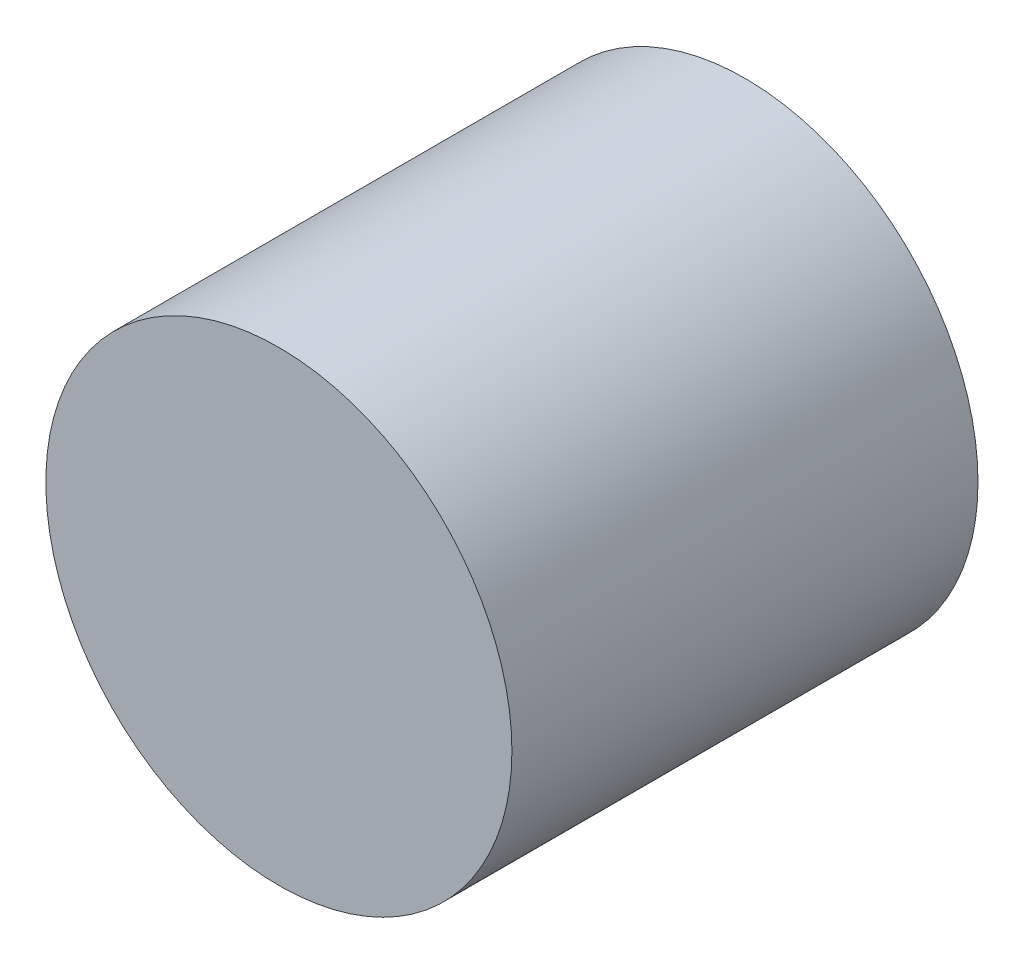
SolidWorks part; units mm, degrees
ref_plane "前视基准面" through (0, 0, 0) normal (0, 0, 1) x (1, 0, 0)
ref_plane "上视基准面" through (0, 0, 0) normal (0, 1, 0) x (1, 0, 0)
ref_plane "右视基准面" through (0, 0, 0) normal (1, 0, 0) x (0, 0, -1)
other "Configuration Table"
sketch "草图1" plane through (0, 0, 0) normal (0, 0, 1) x (1, 0, 0)
  circle A0 centre (137.4892, 29.3655) radius 5
  dimension "D1" = 10
extrude "凸台-拉伸1" add sketch "草图1" along normal blind 10
